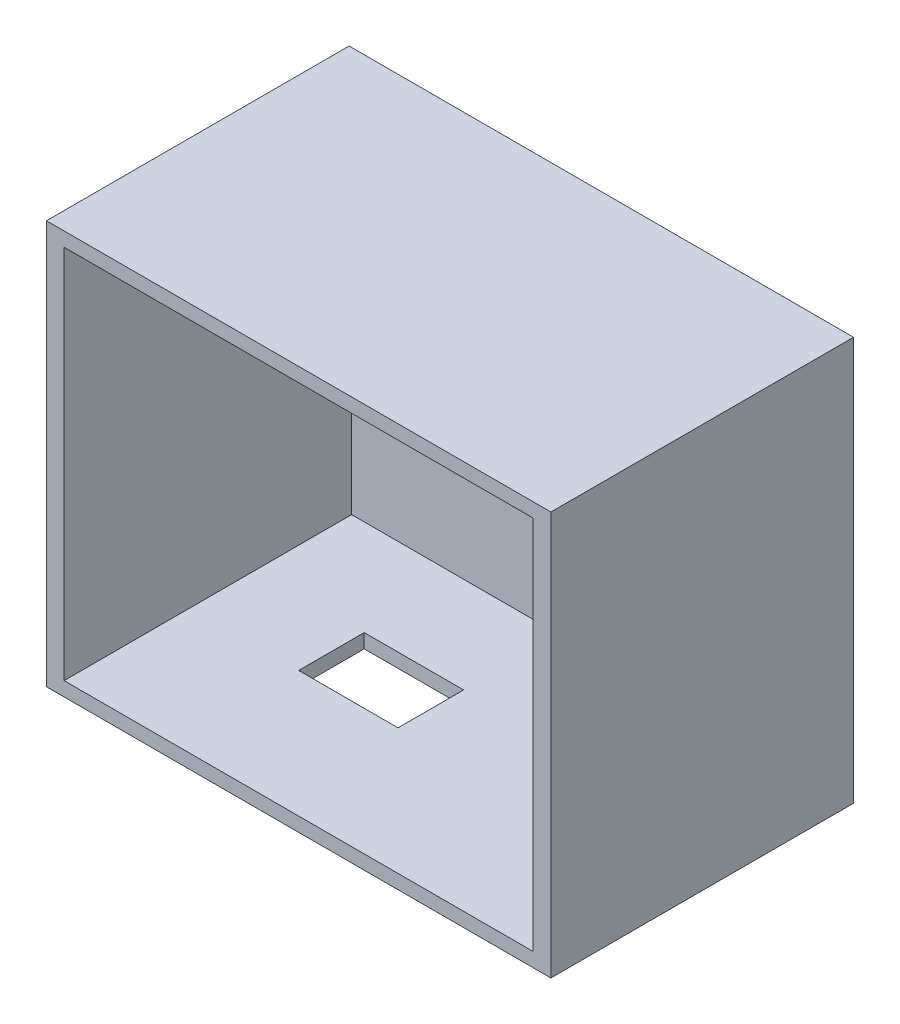
SolidWorks part; units mm, degrees
ref_plane "Plano frontal" through (0, 0, 0) normal (0, 0, 1) x (1, 0, 0)
ref_plane "Plano superior" through (0, 0, 0) normal (0, 1, 0) x (1, 0, 0)
ref_plane "Plano direito" through (0, 0, 0) normal (1, 0, 0) x (0, 0, -1)
sketch "Esboço1" plane through (0, 0, 0) normal (0, 0, 1) x (1, 0, 0)
  line L1 (0, 0) -> (100, 0)
  line L2 (0, 0) -> (0, 80)
  line L3 (0, 80) -> (100, 80)
  line L4 (100, 0) -> (100, 80)
  point P7 (0, 0)
  dimension "D1" = 100
  dimension "D2" = 80
extrude "Ressalto-extrusão1" add sketch "Esboço1" along normal blind 3
sketch "Esboço2" plane through (0, 0, 0) normal (0, 0, 1) x (1, 0, 0)
  line L0 (0, 80) -> (100, 0) construction
  line L1 (0, 80) -> (100, 80)
  line L2 (0, 80) -> (0, 0)
  line L3 (0, 0) -> (100, 0)
  line L4 (100, 80) -> (100, 0)
  line L5 (3.5, 80) -> (3.5, 0) construction
  line L6 (3.5, 0) -> (96.5, 0) construction
  line L7 (96.5, 0) -> (96.5, 80) construction
  line L9 (3.5, 77.2) -> (96.5, 77.2)
  line L10 (3.5, 77.2) -> (3.5, 2.8)
  line L11 (3.5, 2.8) -> (96.5, 2.8)
  line L12 (96.5, 77.2) -> (96.5, 2.8)
  dimension "D1" = 3.5
  dimension "D2" = 3.5
extrude "Ressalto-extrusão2" add sketch "Esboço2" along normal blind 60
sketch "Esboço3" plane through (0, 0, 0) normal (0, 1, 0) x (1, 0, 0)
  line L1 (25, -22) -> (44.7, -22)
  line L2 (25, -22) -> (25, -35)
  line L3 (25, -35) -> (44.7, -35)
  line L4 (44.7, -22) -> (44.7, -35)
  dimension "D1" = 19.7
  dimension "D2" = 13
  dimension "D3" = 25
  dimension "D4" = 25
extrude "Corte-extrusão1" cut sketch "Esboço3" along normal blind 10 and the other way blind 17
